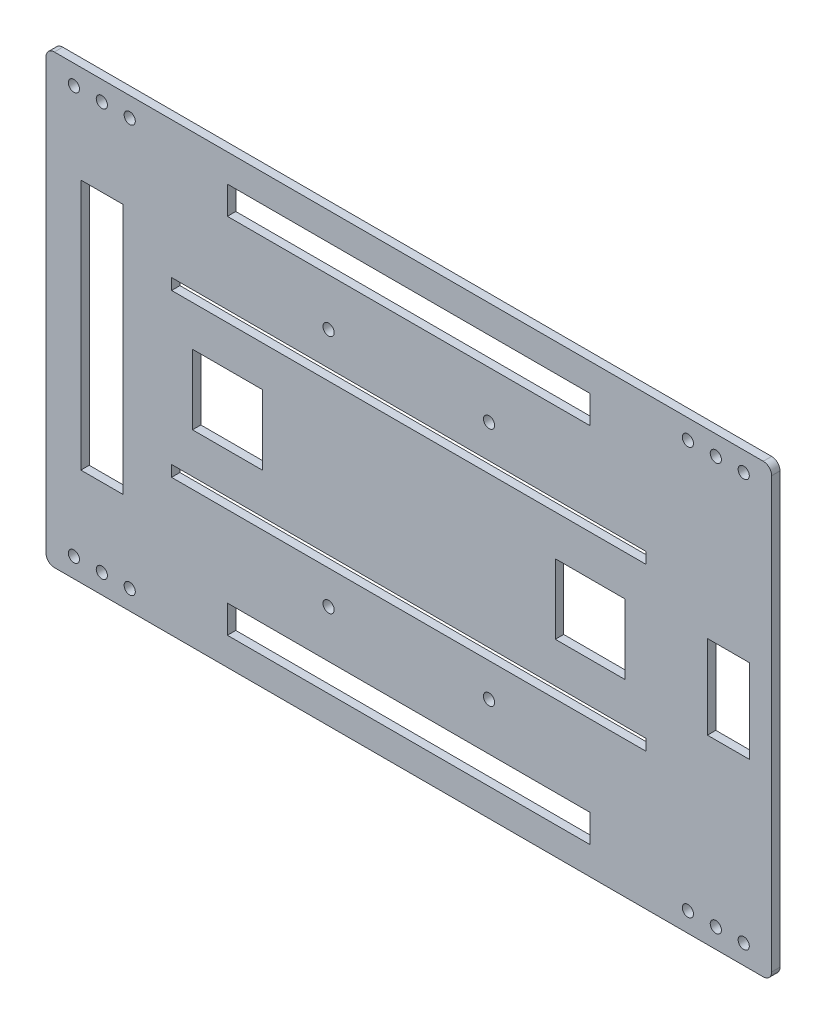
SolidWorks part; units mm, degrees
ref_plane "前视基准面" through (0, 0, 0) normal (0, 0, 1) x (1, 0, 0)
ref_plane "上视基准面" through (0, 0, 0) normal (0, 1, 0) x (1, 0, 0)
ref_plane "右视基准面" through (0, 0, 0) normal (1, 0, 0) x (0, 0, -1)
sketch "Model" plane through (0, 0, 0) normal (0, 0, 1) x (1, 0, 0)
  line L0 (65, 70) -> (-65, 70)
  line L1 (65, 60) -> (65, 70)
  line L2 (-65, 60) -> (65, 60)
  line L3 (-65, 70) -> (-65, 60)
  line L4 (-65, -70) -> (65, -70)
  line L5 (-65, -60) -> (-65, -70)
  line L6 (65, -60) -> (-65, -60)
  line L7 (65, -70) -> (65, -60)
  line L8 (-102.5, 45) -> (-117.5, 45)
  line L9 (-102.5, -45) -> (-102.5, 45)
  line L10 (-117.5, -45) -> (-102.5, -45)
  line L11 (-117.5, 45) -> (-117.5, -45)
  line L12 (77.5, 12.5) -> (52.5, 12.5)
  line L13 (77.5, -12.5) -> (77.5, 12.5)
  line L14 (52.5, -12.5) -> (77.5, -12.5)
  line L15 (52.5, 12.5) -> (52.5, -12.5)
  line L16 (-52.5, 12.5) -> (-77.5, 12.5)
  line L17 (-52.5, -12.5) -> (-52.5, 12.5)
  line L18 (-77.5, -12.5) -> (-52.5, -12.5)
  line L19 (-77.5, 12.5) -> (-77.5, -12.5)
  line L20 (122, 15) -> (107, 15)
  line L21 (122, -15) -> (122, 15)
  line L22 (107, -15) -> (122, -15)
  line L23 (107, 15) -> (107, -15)
  line L24 (85, 31) -> (-85, 31)
  line L25 (85, 27) -> (85, 31)
  line L26 (-85, 27) -> (85, 27)
  line L27 (-85, 31) -> (-85, 27)
  line L28 (85, -27) -> (-85, -27)
  line L29 (85, -31) -> (85, -27)
  line L30 (-85, -31) -> (85, -31)
  line L31 (-85, -27) -> (-85, -31)
  line L32 (130, -77) -> (130, 77)
  line L33 (127, 80) -> (-127, 80)
  line L34 (-130, 77) -> (-130, -77)
  line L35 (-127, -80) -> (127, -80)
  arc A0 (130, 77) -> (127, 80) centre (127, 77) ccw
  arc A1 (-127, 80) -> (-130, 77) centre (-127, 77) ccw
  arc A2 (-130, -77) -> (-127, -80) centre (-127, -77) ccw
  arc A3 (127, -80) -> (130, -77) centre (127, -77) ccw
  circle A4 centre (-110, 73) radius 2
  circle A5 centre (110, 73) radius 2
  circle A6 centre (110, -73) radius 2
  circle A7 centre (-110, -73) radius 2
  circle A8 centre (-120, 73) radius 2
  circle A9 centre (120, 73) radius 2
  circle A10 centre (-120, -73) radius 2
  circle A11 centre (120, -73) radius 2
  circle A12 centre (-100, 73) radius 2
  circle A13 centre (100, 73) radius 2
  circle A14 centre (-100, -73) radius 2
  circle A15 centre (100, -73) radius 2
extrude "凸台-拉伸1" add sketch "Model" along normal blind 3
sketch "草图1" plane through (0, 0, 3) normal (0, 0, 1) x (1, 0, 0)
  line L1 (-28.75, -43) -> (28.75, -43)
  line L2 (-28.75, -43) -> (-28.75, 43)
  line L3 (-28.75, 43) -> (28.75, 43)
  line L4 (28.75, -43) -> (28.75, 43)
  line L5 (-28.75, -43) -> (28.75, 43) construction
  line L6 (-28.75, 43) -> (28.75, -43) construction
  circle A0 centre (-28.75, 43) radius 2
  circle A1 centre (28.75, 43) radius 2
  circle A2 centre (-28.75, -43) radius 2
  circle A3 centre (28.75, -43) radius 2
  point P0 (0, 0)
  dimension "D3" = 4
  dimension "D4" = 4
  dimension "D5" = 4
  dimension "D6" = 4
  dimension "D1" = 86
  dimension "D2" = 57.5
extrude "切除-拉伸1" cut sketch "草图1" against normal blind 10 contours A0 | A2 | A3 | A1
